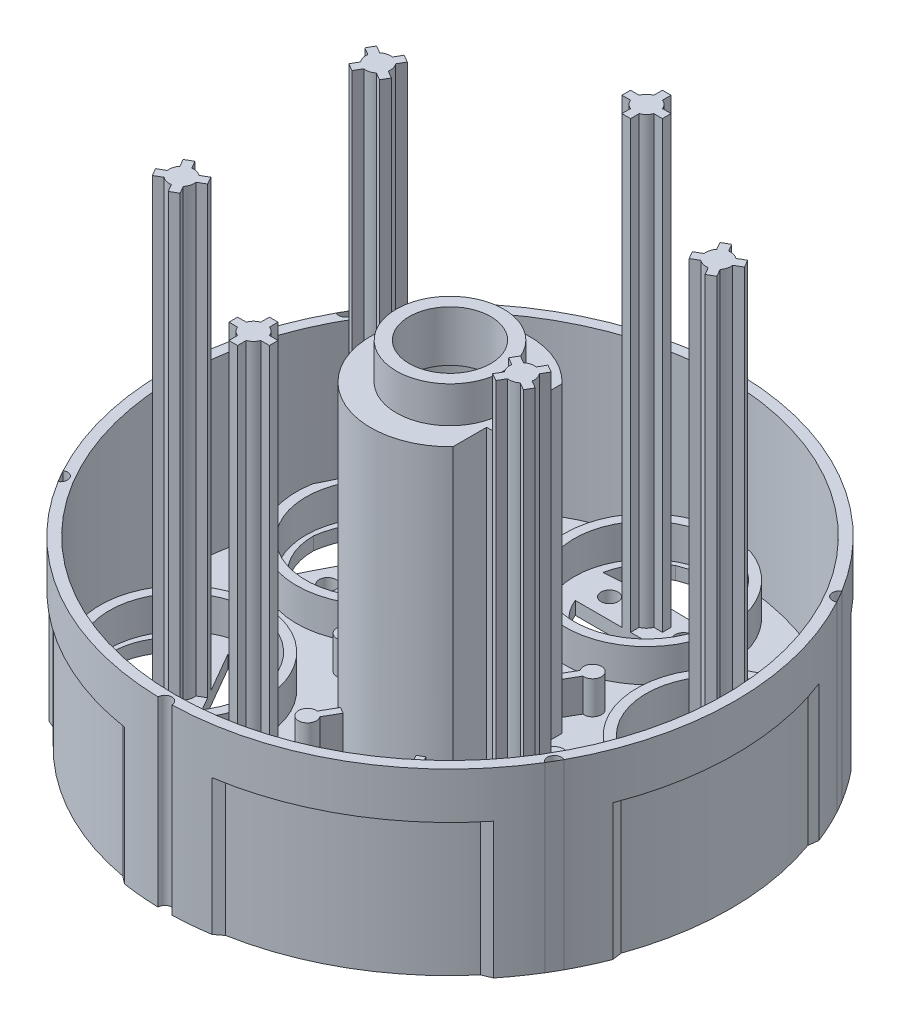
SolidWorks part; units mm, degrees
ref_plane "Front Plane" through (0, 0, 0) normal (0, 0, 1) x (1, 0, 0)
ref_plane "Top Plane" through (0, 0, 0) normal (0, 1, 0) x (1, 0, 0)
ref_plane "Right Plane" through (0, 0, 0) normal (1, 0, 0) x (0, 0, -1)
sketch "Sketch1" plane through (0, 0, 0) normal (0, 1, 0) x (1, 0, 0)
  circle A0 centre (0, 0) radius 30.63
  dimension "D1" = 61.26
extrude "Boss-Extrude1" add sketch "Sketch1" along normal blind 19.56
sketch "Sketch2" plane through (0, 19.56, 0) normal (0, 1, 0) x (1, 0, 0)
  circle A0 centre (0, 0) radius 29.5
  dimension "D1" = 59
extrude "Cut-Extrude1" cut sketch "Sketch2" against normal blind 18.17
sketch "Sketch4" plane through (0, 1.39, 0) normal (0, 1, 0) x (1, 0, 0)
  circle A0 centre (0, 0) radius 8.515
  dimension "D1" = 17.03
extrude "Boss-Extrude2" add sketch "Sketch4" along normal blind 36.43
sketch "Sketch5" plane through (0, 37.82, 0) normal (0, 1, 0) x (1, 0, 0)
  circle A0 centre (0, 0) radius 5.765
  circle A1 centre (0, 0) radius 8.515
  circle A2 centre (0, 0) radius 8.515 construction
  dimension "D1" = 11.53
extrude "Cut-Extrude2" cut sketch "Sketch5" against normal blind 3.9
sketch "Sketch6" plane through (0, 37.82, 0) normal (0, 1, 0) x (1, 0, 0)
  circle A0 centre (0, 0) radius 4.38
  dimension "D1" = 8.76
extrude "Cut-Extrude3" cut sketch "Sketch6" against normal through all
sketch "Sketch7" plane through (0, 33.92, 0) normal (0, 1, 0) x (1, 0, 0)
  line L0 (8.515, -28.7346) -> (8.515, 24.8811) construction
  line L1 (8.2137, 2.245) -> (6.1816, 2.245)
  line L2 (8.2137, -2.245) -> (6.1816, -2.245)
  line L3 (-20.801, 0) -> (20.801, 0) construction
  line L6 (6.1816, 2.245) -> (6.1816, 5.856)
  line L7 (6.1816, -2.245) -> (6.1816, -5.856)
  circle A1 centre (0, 0) radius 8.515 construction
  arc A3 (6.1816, 5.856) -> (8.2137, 2.245) centre (0, 0) cw
  arc A4 (6.1816, -5.856) -> (8.2137, -2.245) centre (0, 0) ccw
  dimension "D1" = 2.245
  dimension "D2" = 2.245
extrude "Cut-Extrude4" cut sketch "Sketch7" against normal up to surface (32.53 mm away) up to face at (0, 1.39, 8.515)
sketch "Sketch8" plane through (0, 0, 0) normal (0, -1, 0) x (1, 0, 0)
  line L0 (7.201, -1.035) -> (6.115, -1.035)
  line L1 (7.201, 1.035) -> (6.115, 1.035)
  line L2 (20.801, 0) -> (-20.801, 0) construction
  line L3 (6.115, -1.035) -> (6.115, -3.9411)
  line L4 (6.115, 1.035) -> (6.115, 3.9411)
  arc A0 (7.201, -1.035) -> (7.201, 1.035) centre (0, 0) ccw
  arc A2 (6.115, 3.9411) -> (6.115, -3.9411) centre (0, 0) ccw
  dimension "D1" = 14.55
  dimension "D2" = 1.035
  dimension "D3" = 1.035
extrude "Cut-Extrude5" cut sketch "Sketch8" against normal blind 32.37
sketch "Sketch9" plane through (0, 1.39, 0) normal (0, 1, 0) x (1, 0, 0)
  line L0 (0, 0) -> (38.677, 0) construction
  line L1 (-20.801, 0) -> (20.801, 0) construction
  line L2 (8.5062, 0.3863) -> (10.339, 0.3863)
  line L3 (8.5062, -0.3863) -> (10.339, -0.3863)
  line L14 (4.5877, -7.1735) -> (5.5041, -8.7607)
  line L15 (3.9186, -7.5598) -> (4.835, -9.147)
  line L16 (-3.9186, -7.5598) -> (-4.835, -9.147)
  line L17 (-4.5877, -7.1735) -> (-5.5041, -8.7607)
  line L18 (-8.5062, -0.3863) -> (-10.339, -0.3863)
  line L19 (-8.5062, 0.3863) -> (-10.339, 0.3863)
  line L20 (-4.5877, 7.1735) -> (-5.5041, 8.7607)
  line L21 (-3.9186, 7.5598) -> (-4.835, 9.147)
  line L22 (3.9186, 7.5598) -> (4.835, 9.147)
  line L23 (4.5877, 7.1735) -> (5.5041, 8.7607)
  arc A0 (10.339, -0.3863) -> (10.339, 0.3863) centre (11.2143, 0) ccw
  arc A1 (8.2137, -2.245) -> (8.2137, 2.245) centre (0, 0) ccw construction
  arc A3 (8.5062, 0.3863) -> (8.5062, -0.3863) centre (0, 0) cw
  arc A4 (4.5877, -7.1735) -> (3.9186, -7.5598) centre (0, 0) cw
  arc A5 (4.835, -9.147) -> (5.5041, -8.7607) centre (5.6071, -9.7119) ccw
  arc A6 (-3.9186, -7.5598) -> (-4.5877, -7.1735) centre (0, 0) cw
  arc A7 (-5.5041, -8.7607) -> (-4.835, -9.147) centre (-5.6071, -9.7119) ccw
  arc A8 (-8.5062, -0.3863) -> (-8.5062, 0.3863) centre (0, 0) cw
  arc A9 (-10.339, 0.3863) -> (-10.339, -0.3863) centre (-11.2143, 0) ccw
  arc A10 (-4.5877, 7.1735) -> (-3.9186, 7.5598) centre (0, 0) cw
  arc A11 (-4.835, 9.147) -> (-5.5041, 8.7607) centre (-5.6071, 9.7119) ccw
  arc A12 (3.9186, 7.5598) -> (4.5877, 7.1735) centre (0, 0) cw
  arc A13 (5.5041, 8.7607) -> (4.835, 9.147) centre (5.6071, 9.7119) ccw
  point P38 (0, 0)
  point P42 (0, 0)
  dimension "D1" = 6
extrude "Boss-Extrude3" add sketch "Sketch9" along normal blind 3.54
sketch "Sketch10" plane through (0, 1.39, 0) normal (0, 1, 0) x (1, 0, 0)
  line L0 (0, -20.801) -> (0, 20.801) construction
  circle A0 centre (0, 21.11) radius 7.75
  circle A1 centre (0, 21.11) radius 8.75
  circle A4 centre (18.2818, 10.555) radius 8.75
  circle A5 centre (18.2818, 10.555) radius 7.75
  circle A6 centre (18.2818, -10.555) radius 8.75
  circle A7 centre (18.2818, -10.555) radius 7.75
  circle A8 centre (0, -21.11) radius 8.75
  circle A9 centre (0, -21.11) radius 7.75
  circle A10 centre (-18.2818, -10.555) radius 8.75
  circle A11 centre (-18.2818, -10.555) radius 7.75
  circle A12 centre (-18.2818, 10.555) radius 8.75
  circle A13 centre (-18.2818, 10.555) radius 7.75
  point P22 (0, 0)
  dimension "D1" = 15.5
  dimension "D2" = 17.5
  dimension "D3" = 6
extrude "Boss-Extrude7" add sketch "Sketch10" along normal up to surface (3.54 mm away) up to face at (-9.8828, 4.93, 0)
sketch "Sketch11" plane through (0, 1.39, 0) normal (0, 1, 0) x (1, 0, 0)
  line L0 (0, -20.801) -> (0, 20.801) construction
  line L2 (-0.465, 19.8639) -> (-0.465, 18.9358)
  line L3 (0.465, 19.8639) -> (0.465, 18.9358)
  line L4 (16.9702, 10.3347) -> (16.1664, 9.8706)
  line L5 (-0.465, 18.9358) -> (0.465, 18.9358)
  line L7 (-1.2461, 21.575) -> (-2.1742, 21.575)
  line L8 (-2.1742, 21.575) -> (-2.1742, 20.645)
  line L9 (-1.2461, 20.645) -> (-2.1742, 20.645)
  line L11 (0.465, 22.3561) -> (0.465, 23.2842)
  line L12 (0.465, 23.2842) -> (-0.465, 23.2842)
  line L13 (-0.465, 22.3561) -> (-0.465, 23.2842)
  line L15 (1.2461, 20.645) -> (2.1742, 20.645)
  line L16 (2.1742, 20.645) -> (2.1742, 21.575)
  line L17 (1.2461, 21.575) -> (2.1742, 21.575)
  line L21 (16.1664, 9.8706) -> (16.6314, 9.0652)
  line L22 (17.4352, 9.5293) -> (16.6314, 9.0652)
  line L23 (18.5021, 9.2434) -> (18.9662, 8.4396)
  line L24 (18.9662, 8.4396) -> (19.7716, 8.9046)
  line L25 (19.3075, 9.7084) -> (19.7716, 8.9046)
  line L26 (19.5934, 10.7753) -> (20.3972, 11.2394)
  line L27 (20.3972, 11.2394) -> (19.9322, 12.0448)
  line L28 (19.1284, 11.5807) -> (19.9322, 12.0448)
  line L29 (18.0615, 11.8666) -> (17.5974, 12.6704)
  line L30 (17.5974, 12.6704) -> (16.792, 12.2054)
  line L31 (17.2561, 11.4016) -> (16.792, 12.2054)
  line L32 (17.4352, -9.5293) -> (16.6314, -9.0652)
  line L33 (16.6314, -9.0652) -> (16.1664, -9.8706)
  line L34 (16.9702, -10.3347) -> (16.1664, -9.8706)
  line L35 (17.2561, -11.4016) -> (16.792, -12.2054)
  line L36 (16.792, -12.2054) -> (17.5974, -12.6704)
  line L37 (18.0615, -11.8666) -> (17.5974, -12.6704)
  line L38 (19.1284, -11.5807) -> (19.9322, -12.0448)
  line L39 (19.9322, -12.0448) -> (20.3972, -11.2394)
  line L40 (19.5934, -10.7753) -> (20.3972, -11.2394)
  line L41 (19.3075, -9.7084) -> (19.7716, -8.9046)
  line L42 (19.7716, -8.9046) -> (18.9662, -8.4396)
  line L43 (18.5021, -9.2434) -> (18.9662, -8.4396)
  line L44 (0.465, -19.8639) -> (0.465, -18.9358)
  line L45 (0.465, -18.9358) -> (-0.465, -18.9358)
  line L46 (-0.465, -19.8639) -> (-0.465, -18.9358)
  line L47 (-1.2461, -20.645) -> (-2.1742, -20.645)
  line L48 (-2.1742, -20.645) -> (-2.1742, -21.575)
  line L49 (-1.2461, -21.575) -> (-2.1742, -21.575)
  line L50 (-0.465, -22.3561) -> (-0.465, -23.2842)
  line L51 (-0.465, -23.2842) -> (0.465, -23.2842)
  line L52 (0.465, -22.3561) -> (0.465, -23.2842)
  line L53 (1.2461, -21.575) -> (2.1742, -21.575)
  line L54 (2.1742, -21.575) -> (2.1742, -20.645)
  line L55 (1.2461, -20.645) -> (2.1742, -20.645)
  line L56 (-16.9702, -10.3347) -> (-16.1664, -9.8706)
  line L57 (-16.1664, -9.8706) -> (-16.6314, -9.0652)
  line L58 (-17.4352, -9.5293) -> (-16.6314, -9.0652)
  line L59 (-18.5021, -9.2434) -> (-18.9662, -8.4396)
  line L60 (-18.9662, -8.4396) -> (-19.7716, -8.9046)
  line L61 (-19.3075, -9.7084) -> (-19.7716, -8.9046)
  line L62 (-19.5934, -10.7753) -> (-20.3972, -11.2394)
  line L63 (-20.3972, -11.2394) -> (-19.9322, -12.0448)
  line L64 (-19.1284, -11.5807) -> (-19.9322, -12.0448)
  line L65 (-18.0615, -11.8666) -> (-17.5974, -12.6704)
  line L66 (-17.5974, -12.6704) -> (-16.792, -12.2054)
  line L67 (-17.2561, -11.4016) -> (-16.792, -12.2054)
  line L68 (-17.4352, 9.5293) -> (-16.6314, 9.0652)
  line L69 (-16.6314, 9.0652) -> (-16.1664, 9.8706)
  line L70 (-16.9702, 10.3347) -> (-16.1664, 9.8706)
  line L71 (-17.2561, 11.4016) -> (-16.792, 12.2054)
  line L72 (-16.792, 12.2054) -> (-17.5974, 12.6704)
  line L73 (-18.0615, 11.8666) -> (-17.5974, 12.6704)
  line L74 (-19.1284, 11.5807) -> (-19.9322, 12.0448)
  line L75 (-19.9322, 12.0448) -> (-20.3972, 11.2394)
  line L76 (-19.5934, 10.7753) -> (-20.3972, 11.2394)
  line L77 (-19.3075, 9.7084) -> (-19.7716, 8.9046)
  line L78 (-19.7716, 8.9046) -> (-18.9662, 8.4396)
  line L79 (-18.5021, 9.2434) -> (-18.9662, 8.4396)
  arc A1 (-1.2461, 20.645) -> (-0.465, 19.8639) centre (0, 21.11) ccw
  arc A2 (1.2461, 21.575) -> (0.465, 22.3561) centre (0, 21.11) ccw
  arc A3 (-0.465, 22.3561) -> (-1.2461, 21.575) centre (0, 21.11) ccw
  circle A4 centre (0, 21.11) radius 7.75 construction
  arc A5 (0.465, 19.8639) -> (1.2461, 20.645) centre (0, 21.11) ccw
  arc A6 (17.4352, 9.5293) -> (18.5021, 9.2434) centre (18.2818, 10.555) ccw
  arc A7 (19.3075, 9.7084) -> (19.5934, 10.7753) centre (18.2818, 10.555) ccw
  arc A8 (19.1284, 11.5807) -> (18.0615, 11.8666) centre (18.2818, 10.555) ccw
  arc A9 (17.2561, 11.4016) -> (16.9702, 10.3347) centre (18.2818, 10.555) ccw
  arc A10 (16.9702, -10.3347) -> (17.2561, -11.4016) centre (18.2818, -10.555) ccw
  arc A11 (18.0615, -11.8666) -> (19.1284, -11.5807) centre (18.2818, -10.555) ccw
  arc A12 (19.5934, -10.7753) -> (19.3075, -9.7084) centre (18.2818, -10.555) ccw
  arc A13 (18.5021, -9.2434) -> (17.4352, -9.5293) centre (18.2818, -10.555) ccw
  arc A14 (-0.465, -19.8639) -> (-1.2461, -20.645) centre (0, -21.11) ccw
  arc A15 (-1.2461, -21.575) -> (-0.465, -22.3561) centre (0, -21.11) ccw
  arc A16 (0.465, -22.3561) -> (1.2461, -21.575) centre (0, -21.11) ccw
  arc A17 (1.2461, -20.645) -> (0.465, -19.8639) centre (0, -21.11) ccw
  arc A18 (-17.4352, -9.5293) -> (-18.5021, -9.2434) centre (-18.2818, -10.555) ccw
  arc A19 (-19.3075, -9.7084) -> (-19.5934, -10.7753) centre (-18.2818, -10.555) ccw
  arc A20 (-19.1284, -11.5807) -> (-18.0615, -11.8666) centre (-18.2818, -10.555) ccw
  arc A21 (-17.2561, -11.4016) -> (-16.9702, -10.3347) centre (-18.2818, -10.555) ccw
  arc A22 (-16.9702, 10.3347) -> (-17.2561, 11.4016) centre (-18.2818, 10.555) ccw
  arc A23 (-18.0615, 11.8666) -> (-19.1284, 11.5807) centre (-18.2818, 10.555) ccw
  arc A24 (-19.5934, 10.7753) -> (-19.3075, 9.7084) centre (-18.2818, 10.555) ccw
  arc A25 (-18.5021, 9.2434) -> (-17.4352, 9.5293) centre (-18.2818, 10.555) ccw
  point P25 (0, 21.11)
  point P115 (0, 0)
  dimension "D1" = 2.66
  dimension "D2" = 4
  dimension "D3" = 6
extrude "Boss-Extrude9" add sketch "Sketch11" along normal blind 47.8
sketch "Sketch13" plane through (0, 1.39, 0) normal (0, 1, 0) x (1, 0, 0)
  line L0 (-5.48, 18.9358) -> (5.48, 18.9358)
  line L1 (0, 24.4264) -> (0, 17.4063) construction
  line L2 (0, -27.0545) -> (0, 27.0545) construction
  line L3 (13.6589, 14.2137) -> (19.1389, 4.7221)
  line L4 (19.1389, -4.7221) -> (13.6589, -14.2137)
  line L5 (0, 31.957) -> (0, 11.4499) construction
  line L6 (5.48, -18.9358) -> (-5.48, -18.9358)
  line L7 (-13.6589, -14.2137) -> (-19.1389, -4.7221)
  line L8 (-19.1389, 4.7221) -> (-13.6589, 14.2137)
  arc A0 (-5.48, 18.9358) -> (5.48, 18.9358) centre (0, 21.11) ccw
  circle A1 centre (0, 21.11) radius 7.75 construction
  arc A2 (-6.59, 23.0224) -> (6.59, 23.0197) centre (-0.0166, -59.3613) cw
  arc A3 (-3.328, 27.5746) -> (3.328, 27.5746) centre (0, 19.327) cw
  arc A4 (-6.59, 23.0224) -> (-3.328, 27.5746) centre (0.0105, 21.7374) cw
  arc A5 (6.59, 23.0197) -> (3.328, 27.5746) centre (0.3249, 21.9784) ccw
  circle A6 centre (-3.9699, 21.11) radius 0.9096
  circle A7 centre (3.9699, 21.11) radius 0.9096
  arc A8 (23.2307, 5.8027) -> (25.5442, 10.9052) centre (19.1963, 10.7078) ccw
  arc A9 (22.2163, 16.6694) -> (25.5442, 10.9052) centre (16.7376, 9.6635) cw
  arc A10 (16.643, 17.2183) -> (22.2163, 16.6694) centre (18.8304, 10.8596) cw
  arc A11 (16.643, 17.2183) -> (23.2307, 5.8027) centre (-51.4167, -29.6662) cw
  circle A12 centre (16.2969, 13.993) radius 0.9096
  circle A13 centre (20.2667, 7.117) radius 0.9096
  arc A14 (13.6589, 14.2137) -> (19.1389, 4.7221) centre (18.2818, 10.555) ccw
  arc A15 (16.6407, -17.217) -> (22.2163, -16.6694) centre (18.8714, -11.2706) ccw
  arc A16 (25.5442, -10.9052) -> (22.2163, -16.6694) centre (16.7376, -9.6635) cw
  arc A17 (23.233, -5.8041) -> (25.5442, -10.9052) centre (18.8198, -10.8778) cw
  arc A18 (23.233, -5.8041) -> (16.6407, -17.217) centre (-51.4001, 29.6951) cw
  circle A19 centre (20.2667, -7.117) radius 0.9096
  circle A20 centre (16.2969, -13.993) radius 0.9096
  arc A21 (19.1389, -4.7221) -> (13.6589, -14.2137) centre (18.2818, -10.555) ccw
  arc A22 (-6.59, -23.0197) -> (-3.328, -27.5746) centre (-0.3249, -21.9784) ccw
  arc A23 (3.328, -27.5746) -> (-3.328, -27.5746) centre (0, -19.327) cw
  arc A24 (6.59, -23.0224) -> (3.328, -27.5746) centre (-0.0105, -21.7374) cw
  arc A25 (6.59, -23.0224) -> (-6.59, -23.0197) centre (0.0166, 59.3613) cw
  circle A26 centre (3.9699, -21.11) radius 0.9096
  circle A27 centre (-3.9699, -21.11) radius 0.9096
  arc A28 (5.48, -18.9358) -> (-5.48, -18.9358) centre (0, -21.11) ccw
  arc A29 (-23.2307, -5.8027) -> (-25.5442, -10.9052) centre (-19.1963, -10.7078) ccw
  arc A30 (-22.2163, -16.6694) -> (-25.5442, -10.9052) centre (-16.7376, -9.6635) cw
  arc A31 (-16.643, -17.2183) -> (-22.2163, -16.6694) centre (-18.8304, -10.8596) cw
  arc A32 (-16.643, -17.2183) -> (-23.2307, -5.8027) centre (51.4167, 29.6662) cw
  circle A33 centre (-16.2969, -13.993) radius 0.9096
  circle A34 centre (-20.2667, -7.117) radius 0.9096
  arc A35 (-13.6589, -14.2137) -> (-19.1389, -4.7221) centre (-18.2818, -10.555) ccw
  arc A36 (-16.6407, 17.217) -> (-22.2163, 16.6694) centre (-18.8714, 11.2706) ccw
  arc A37 (-25.5442, 10.9052) -> (-22.2163, 16.6694) centre (-16.7376, 9.6635) cw
  arc A38 (-23.233, 5.8041) -> (-25.5442, 10.9052) centre (-18.8198, 10.8778) cw
  arc A39 (-23.233, 5.8041) -> (-16.6407, 17.217) centre (51.4001, -29.6951) cw
  circle A40 centre (-20.2667, 7.117) radius 0.9096
  circle A41 centre (-16.2969, 13.993) radius 0.9096
  arc A42 (-19.1389, 4.7221) -> (-13.6589, 14.2137) centre (-18.2818, 10.555) ccw
  point P102 (0, 0)
  dimension "D1" = 5.48
  dimension "D2" = 6.59
  dimension "D3" = 6.59
  dimension "D4" = 6
extrude "Cut-Extrude8" cut sketch "Sketch13" against normal through all
sketch "Sketch14" plane through (0, 0, 0) normal (0, -1, 0) x (1, 0, 0)
  line L1 (5.527, 29.6272) -> (4.6919, 30.2685)
  line L2 (0, -27.0545) -> (0, 27.0545) construction
  line L3 (-5.527, 29.6272) -> (-4.6919, 30.2685)
  line L4 (22.8943, 19.6001) -> (23.8674, 19.1975)
  line L5 (28.4214, 10.027) -> (28.5592, 11.071)
  line L7 (28.4214, -10.027) -> (28.5592, -11.071)
  line L8 (22.8943, -19.6001) -> (23.8674, -19.1975)
  line L10 (5.527, -29.6272) -> (4.6919, -30.2685)
  line L11 (-5.527, -29.6272) -> (-4.6919, -30.2685)
  line L13 (-22.8943, -19.6001) -> (-23.8674, -19.1975)
  line L14 (-28.4214, -10.027) -> (-28.5592, -11.071)
  line L16 (-28.4214, 10.027) -> (-28.5592, 11.071)
  line L17 (-22.8943, 19.6001) -> (-23.8674, 19.1975)
  circle A1 centre (0, 0) radius 30.63 construction
  arc A7 (-22.8943, 19.6001) -> (-5.527, 29.6272) centre (-0.2066, 0.3578) cw
  arc A8 (-23.8674, 19.1975) -> (-4.6919, 30.2685) centre (0, 0) cw
  arc A9 (4.6919, 30.2685) -> (23.8674, 19.1975) centre (0, 0) cw
  arc A10 (5.527, 29.6272) -> (22.8943, 19.6001) centre (0.2066, 0.3578) cw
  arc A11 (28.5592, 11.071) -> (28.5592, -11.071) centre (0, 0) cw
  arc A12 (28.4214, 10.027) -> (28.4214, -10.027) centre (0.4132, 0) cw
  arc A13 (23.8674, -19.1975) -> (4.6919, -30.2685) centre (0, 0) cw
  arc A14 (22.8943, -19.6001) -> (5.527, -29.6272) centre (0.2066, -0.3578) cw
  arc A15 (-4.6919, -30.2685) -> (-23.8674, -19.1975) centre (0, 0) cw
  arc A16 (-5.527, -29.6272) -> (-22.8943, -19.6001) centre (-0.2066, -0.3578) cw
  arc A17 (-28.5592, -11.071) -> (-28.5592, 11.071) centre (0, 0) cw
  arc A18 (-28.4214, -10.027) -> (-28.4214, 10.027) centre (-0.4132, 0) cw
  point P48 (0, 0)
  point P76 (0, 0)
  dimension "D1" = 6
  dimension "D2" = 6
extrude "Cut-Extrude10" cut sketch "Sketch14" against normal blind 14.59
sketch "Sketch16" plane through (0, 0, 0) normal (0, -1, 0) x (1, 0, 0)
  line L1 (26.1438, 15.9592) -> (26.893, 14.6616)
  line L2 (26.893, -14.6616) -> (26.1438, -15.9592)
  line L3 (0.7492, -30.6208) -> (-0.7492, -30.6208)
  line L4 (-26.1438, -15.9592) -> (-26.893, -14.6616)
  line L5 (-26.893, 14.6616) -> (-26.1438, 15.9592)
  line L6 (-0.7492, 30.6208) -> (-0.7492, 30.8649)
  line L7 (-0.7492, 30.8649) -> (0.7492, 30.8649)
  line L8 (0.7492, 30.8649) -> (0.7492, 30.6208)
  arc A0 (-0.7492, 30.6208) -> (0.7492, 30.6208) centre (0, 30.63) ccw
  arc A2 (4.6919, 30.2685) -> (-4.6919, 30.2685) centre (0, 0) ccw construction
  arc A3 (26.1438, 15.9592) -> (26.893, 14.6616) centre (26.5264, 15.315) ccw
  arc A4 (26.893, -14.6616) -> (26.1438, -15.9592) centre (26.5264, -15.315) ccw
  arc A5 (0.7492, -30.6208) -> (-0.7492, -30.6208) centre (0, -30.63) ccw
  arc A6 (-26.1438, -15.9592) -> (-26.893, -14.6616) centre (-26.5264, -15.315) ccw
  arc A7 (-26.893, 14.6616) -> (-26.1438, 15.9592) centre (-26.5264, 15.315) ccw
  point P28 (0, 0)
  dimension "D1" = 6
extrude "Cut-Extrude11" cut sketch "Sketch16" against normal through all
